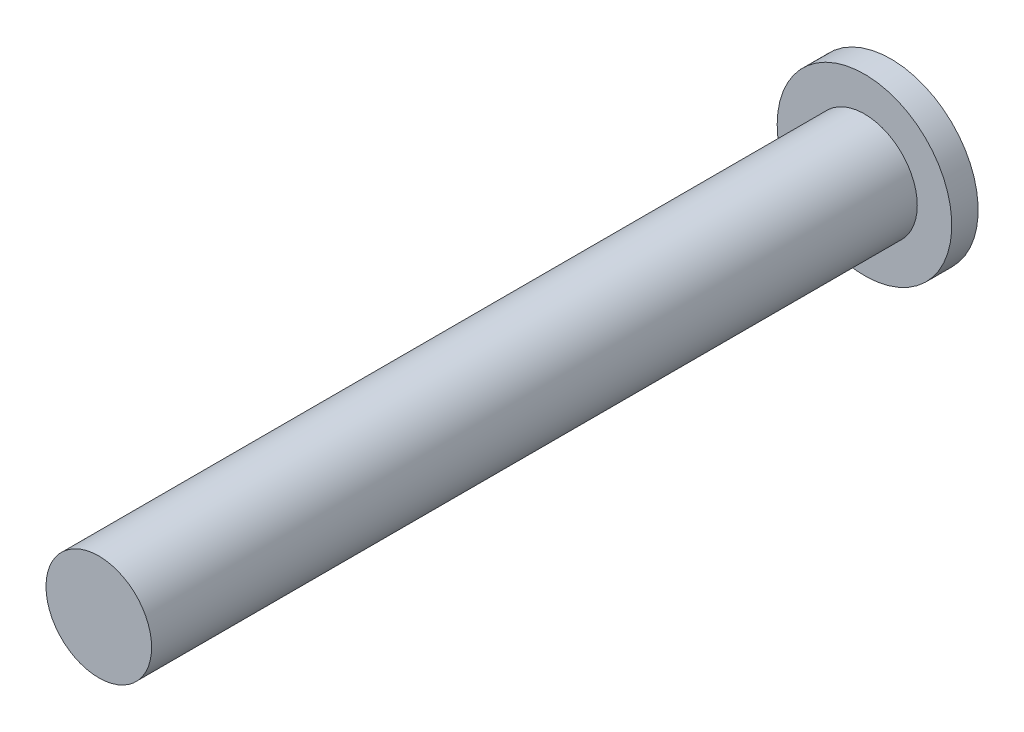
SolidWorks part; units mm, degrees
ref_plane "Front Plane" through (0, 0, 0) normal (0, 0, 1) x (1, 0, 0)
ref_plane "Top Plane" through (0, 0, 0) normal (0, 1, 0) x (1, 0, 0)
ref_plane "Right Plane" through (0, 0, 0) normal (1, 0, 0) x (0, 0, -1)
sketch "Sketch1" plane through (0, 0, 28) normal (0, 0, -1) x (-1, 0, 0)
  circle A1 centre (17.5, 6.1225) radius 4
  circle A2 centre (17.5, 6.1225) radius 4
  dimension "D1" = 0
extrude "Boss-Extrude1" add sketch "Sketch1" along normal up to surface (58 mm away)
sketch "Sketch2" plane through (0, 0, -30) normal (0, 0, -1) x (-1, 0, 0)
  circle A0 centre (17.5, 6.1225) radius 6.6132
extrude "Boss-Extrude2" add sketch "Sketch2" along normal blind 2
